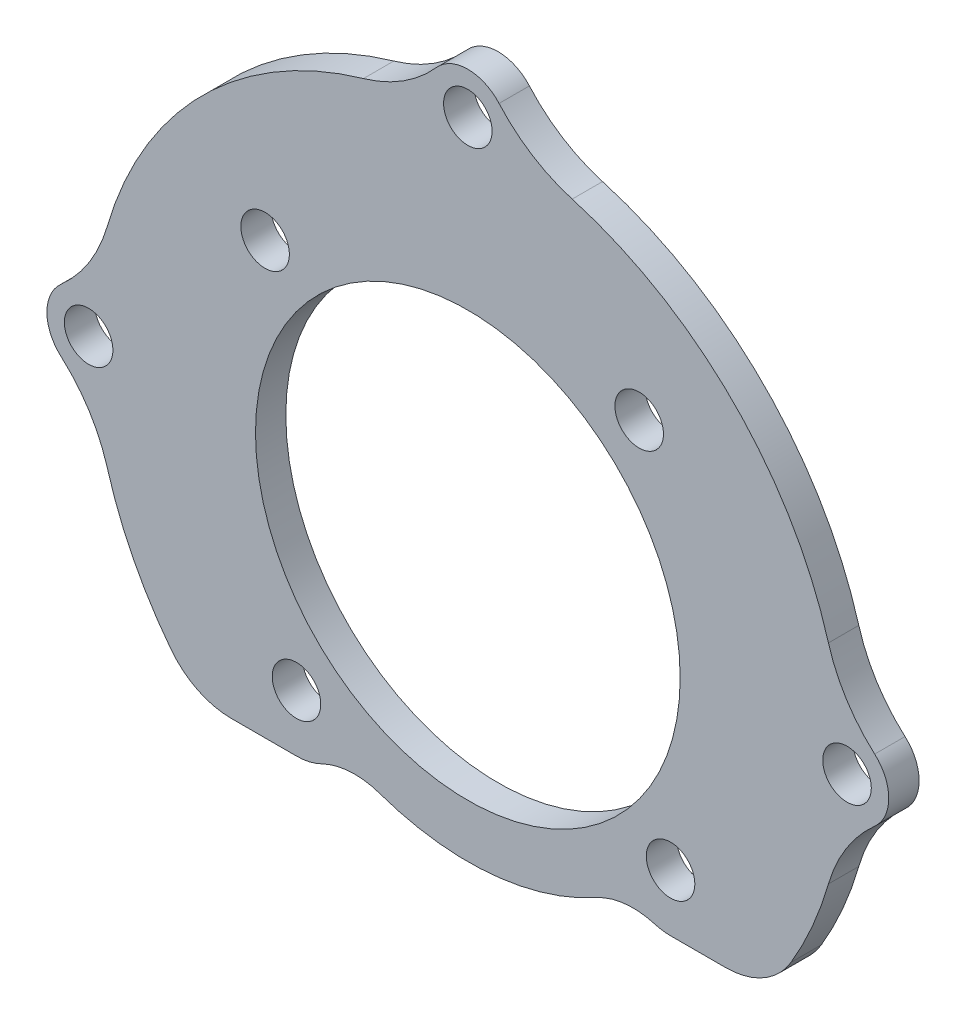
SolidWorks part; units mm, degrees
material "Thornel Mat VMA"
ref_plane "Front Plane" through (0, 0, 0) normal (0, 0, 1) x (1, 0, 0)
ref_plane "Top Plane" through (0, 0, 0) normal (0, 1, 0) x (1, 0, 0)
ref_plane "Right Plane" through (0, 0, 0) normal (1, 0, 0) x (0, 0, -1)
sketch "Sketch1" plane through (0, 0, 0) normal (0, 0, 1) x (1, 0, 0)
  circle A1 centre (0, -40.1) radius 3
  circle A2 centre (0, -40.1) radius 3
  circle A3 centre (-50, -40.1) radius 3
  circle A4 centre (-50, -40.1) radius 3
  circle A5 centre (-25, -15.1) radius 3
  circle A6 centre (-25, -15.1) radius 3
  circle A7 centre (-25, -40.1) radius 25
  circle A8 centre (-25, -40.1) radius 25
  dimension "D1" = 0
  dimension "D2" = 0
  dimension "D3" = 0
  dimension "D4" = 0
extrude "Boss-Extrude1" add sketch "Sketch1" along normal blind 2 contours A8 A4 | A4 A8 | A2 A8 A6 A4 | A8 A6 | A6 A8 | A8 A2 | A2 A8
fillet "Fillet1" radius 10 6 edges at (-0.18, -37.1054, 1) (-0.18, -43.0946, 1) (-49.82, -43.0946, 1) (-49.82, -37.1054, 1) (-27.9946, -15.28, 1) (-22.0054, -15.28, 1)
sketch "Sketch3" plane through (0, 0, 2) normal (0, 0, 1) x (1, 0, 0)
  arc A2 (-37.2167, -29.7679) -> (-39.5149, -27.8396) centre (-38.3658, -28.8037) ccw
  arc A3 (-39.5149, -27.8396) -> (-37.2167, -29.7679) centre (-38.3658, -28.8037) ccw
  arc A4 (-37.2167, -29.7679) -> (-39.5149, -27.8396) centre (-38.3658, -28.8037) ccw
  arc A5 (-39.5149, -27.8396) -> (-37.2167, -29.7679) centre (-38.3658, -28.8037) ccw
  arc A6 (-35.3321, -52.3167) -> (-37.2604, -54.6149) centre (-36.2963, -53.4658) ccw
  arc A7 (-37.2604, -54.6149) -> (-35.3321, -52.3167) centre (-36.2963, -53.4658) ccw
  arc A8 (-35.3321, -52.3167) -> (-37.2604, -54.6149) centre (-36.2963, -53.4658) ccw
  arc A9 (-37.2604, -54.6149) -> (-35.3321, -52.3167) centre (-36.2963, -53.4658) ccw
  arc A10 (-12.7833, -50.4321) -> (-10.4851, -52.3604) centre (-11.6342, -51.3963) ccw
  arc A11 (-10.4851, -52.3604) -> (-12.7833, -50.4321) centre (-11.6342, -51.3963) ccw
  arc A12 (-12.7833, -50.4321) -> (-10.4851, -52.3604) centre (-11.6342, -51.3963) ccw
  arc A13 (-10.4851, -52.3604) -> (-12.7833, -50.4321) centre (-11.6342, -51.3963) ccw
  arc A14 (-14.6679, -27.8833) -> (-12.7396, -25.5851) centre (-13.7037, -26.7342) ccw
  arc A15 (-12.7396, -25.5851) -> (-14.6679, -27.8833) centre (-13.7037, -26.7342) ccw
  arc A16 (-14.6679, -27.8833) -> (-12.7396, -25.5851) centre (-13.7037, -26.7342) ccw
  arc A17 (-12.7396, -25.5851) -> (-14.6679, -27.8833) centre (-13.7037, -26.7342) ccw
  arc A18 (-35.265, -31.4866) -> (-14.735, -48.7134) centre (-25, -40.1) ccw
  arc A19 (-14.735, -48.7134) -> (-35.265, -31.4866) centre (-25, -40.1) ccw
  arc A20 (-35.265, -31.4866) -> (-14.735, -48.7134) centre (-25, -40.1) ccw
  arc A21 (-14.735, -48.7134) -> (-35.265, -31.4866) centre (-25, -40.1) ccw
  dimension "D1" = 0
  dimension "D2" = 0
  dimension "D3" = 0
  dimension "D4" = 0
  dimension "D5" = 0
extrude "Cut-Extrude1" cut sketch "Sketch3" against normal through all
sketch "Sketch4" plane through (0, 0, 2) normal (0, 0, 1) x (1, 0, 0)
  circle A0 centre (-36.2963, -53.4658) radius 1.6
  circle A1 centre (-38.3658, -28.8037) radius 1.6
  circle A2 centre (-13.7037, -26.7342) radius 1.6
  circle A3 centre (-11.6342, -51.3963) radius 1.6
  circle A4 centre (-11.6342, -51.3963) radius 1.5 construction
  circle A5 centre (-25, -40.1) radius 14
  circle A6 centre (-25, -40.1) radius 13.4 construction
  dimension "D1" = 3.2
  dimension "D2" = 28
extrude "Cut-Extrude2" cut sketch "Sketch4" against normal through all
sketch "Sketch5" plane through (0, 0, 2) normal (0, 0, 1) x (1, 0, 0)
  line L2 (-6.6697, -58.7) -> (5, -58.7)
  line L3 (5, -55.5) -> (-6.6697, -55.5)
  line L6 (-6.6697, -58.7) -> (5, -58.7)
  line L7 (5, -55.5) -> (-6.6697, -55.5)
  circle A1 centre (-25, -15.1) radius 2.5
  circle A3 centre (-25, -15.1) radius 2.5
  circle A5 centre (0, -40.1) radius 2.5
  circle A7 centre (0, -40.1) radius 2.5
  circle A9 centre (-50, -40.1) radius 2.5
  circle A10 centre (-50, -40.1) radius 2.5
  circle A11 centre (-54.5, -57.1) radius 1.6
  circle A12 centre (-54.5, -57.1) radius 1.6
  arc A14 (-6.6697, -55.5) -> (-6.6697, -58.7) centre (-6.6697, -57.1) ccw
  arc A15 (5, -58.7) -> (5, -55.5) centre (5, -57.1) ccw
  arc A16 (-6.6697, -55.5) -> (-6.6697, -58.7) centre (-6.6697, -57.1) ccw
  arc A17 (5, -58.7) -> (5, -55.5) centre (5, -57.1) ccw
  dimension "D1" = 0
  dimension "D2" = 0
  dimension "D3" = 0
  dimension "D4" = 0
  dimension "D5" = 0
sketch "Sketch6" plane through (0, 0, 2) normal (0, 0, 1) x (1, 0, 0)
  circle A0 centre (-50, -40.1) radius 1.6
  circle A1 centre (-25, -15.1) radius 1.6
  circle A2 centre (0, -40.1) radius 1.6
  dimension "D1" = 3.2
extrude "Cut-Extrude3" cut sketch "Sketch6" against normal through all
sketch "Sketch7" plane through (0, 0, 2) normal (0, 0, 1) x (1, 0, 0)
  arc A24 (-31.8813, -16.3259) -> (-48.7741, -33.2187) centre (-25, -40.1) ccw
  arc A25 (-51.8235, -38.0415) -> (-48.7741, -33.2187) centre (-58.62, -30.3688) ccw
  arc A26 (-51.8235, -38.0415) -> (-51.8235, -42.1585) centre (-50, -40.1) ccw
  arc A27 (-48.7741, -46.9813) -> (-51.8235, -42.1585) centre (-58.62, -49.8312) ccw
  arc A28 (-48.7741, -46.9813) -> (-1.2259, -46.9813) centre (-25, -40.1) ccw
  arc A29 (1.8235, -42.1585) -> (-1.2259, -46.9813) centre (8.62, -49.8312) ccw
  arc A30 (1.8235, -42.1585) -> (1.8235, -38.0415) centre (0, -40.1) ccw
  arc A31 (-1.2259, -33.2187) -> (1.8235, -38.0415) centre (8.62, -30.3688) ccw
  arc A32 (-1.2259, -33.2187) -> (-18.1187, -16.3259) centre (-25, -40.1) ccw
  arc A33 (-22.9415, -13.2765) -> (-18.1187, -16.3259) centre (-15.2688, -6.48) ccw
  arc A34 (-22.9415, -13.2765) -> (-27.0585, -13.2765) centre (-25, -15.1) ccw
  arc A35 (-31.8813, -16.3259) -> (-27.0585, -13.2765) centre (-34.7312, -6.48) ccw
  arc A36 (-31.8813, -16.3259) -> (-48.7741, -33.2187) centre (-25, -40.1) ccw
  arc A37 (-51.8235, -38.0415) -> (-48.7741, -33.2187) centre (-58.62, -30.3688) ccw
  arc A38 (-51.8235, -38.0415) -> (-51.8235, -42.1585) centre (-50, -40.1) ccw
  arc A39 (-48.7741, -46.9813) -> (-51.8235, -42.1585) centre (-58.62, -49.8312) ccw
  arc A40 (-48.7741, -46.9813) -> (-1.2259, -46.9813) centre (-25, -40.1) ccw
  arc A41 (1.8235, -42.1585) -> (-1.2259, -46.9813) centre (8.62, -49.8312) ccw
  arc A42 (1.8235, -42.1585) -> (1.8235, -38.0415) centre (0, -40.1) ccw
  arc A43 (-1.2259, -33.2187) -> (1.8235, -38.0415) centre (8.62, -30.3688) ccw
  arc A44 (-1.2259, -33.2187) -> (-18.1187, -16.3259) centre (-25, -40.1) ccw
  arc A45 (-22.9415, -13.2765) -> (-18.1187, -16.3259) centre (-15.2688, -6.48) ccw
  arc A46 (-22.9415, -13.2765) -> (-27.0585, -13.2765) centre (-25, -15.1) ccw
  arc A47 (-31.8813, -16.3259) -> (-27.0585, -13.2765) centre (-34.7312, -6.48) ccw
  dimension "D1" = 0.25
extrude "Cut-Extrude4" cut sketch "Sketch7" against normal blind 10 flip side to cut
sketch "Sketch8" plane through (0, 0, 2) normal (0, 0, 1) x (1, 0, 0)
  line L1 (-36.2963, -57.2158) -> (-42.8777, -57.2158)
  line L2 (-11.6342, -55.1463) -> (-5.3487, -55.1463)
  circle A0 centre (-25, -40.1) radius 17.5
  circle A1 centre (-36.2963, -53.4658) radius 3.75
  circle A2 centre (-11.6342, -51.3963) radius 3.75
  arc A5 (-48.7741, -46.9813) -> (-1.2259, -46.9813) centre (-25, -40.1) ccw construction
  arc A6 (-48.7741, -46.9813) -> (-1.2259, -46.9813) centre (-25, -40.1) ccw
  arc M18 (-48.7741, -46.9813) -> (-1.2259, -46.9813) centre (-25, -40.1) ccw
  dimension "D1" = 7.5
extrude "Cut-Extrude5" cut sketch "Sketch8" against normal blind 10 contours A2 A0 A1 L1 L2 M18
fillet "Fillet2" radius 5 4 edges at (-42.8777, -57.2158, 1) (-5.3487, -55.1463, 1) (-14.3478, -53.9845, 1) (-33.1893, -55.5656, 1)
